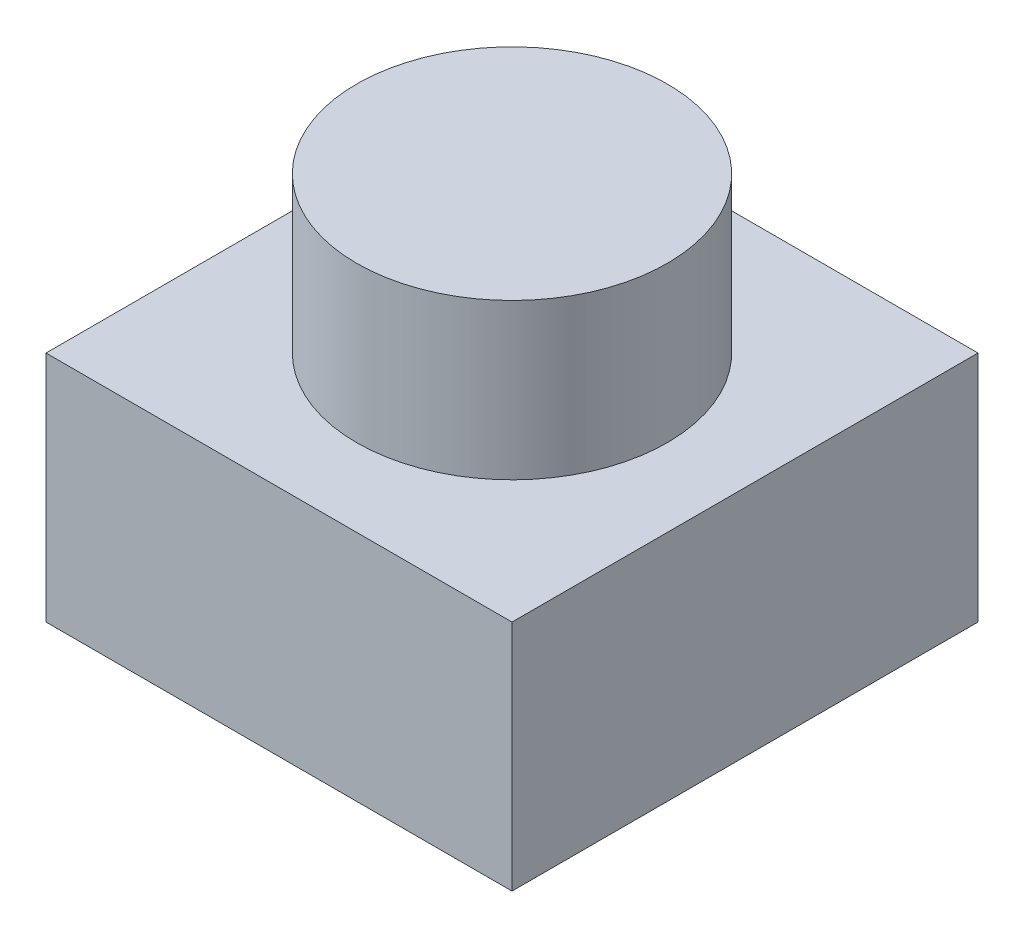
SolidWorks part; units mm, degrees
ref_plane "Front Plane" through (0, 0, 0) normal (0, 0, 1) x (1, 0, 0)
ref_plane "Top Plane" through (0, 0, 0) normal (0, 1, 0) x (1, 0, 0)
ref_plane "Right Plane" through (0, 0, 0) normal (1, 0, 0) x (0, 0, -1)
sketch "Sketch1" plane through (0, 0, 0) normal (0, 1, 0) x (1, 0, 0)
  line L1 (-3, -3) -> (3, -3)
  line L2 (-3, -3) -> (-3, 3)
  line L3 (-3, 3) -> (3, 3)
  line L4 (3, -3) -> (3, 3)
  line L5 (-3, -3) -> (3, 3) construction
  line L6 (-3, 3) -> (3, -3) construction
  point P0 (0, 0)
  dimension "D1" = 6
  dimension "D2" = 6
extrude "Boss-Extrude1" add sketch "Sketch1" along normal blind 3
sketch "Sketch2" plane through (0, 3, 0) normal (0, 1, 0) x (1, 0, 0)
  circle A0 centre (0, 0) radius 2
  dimension "D1" = 4
extrude "Boss-Extrude2" add sketch "Sketch2" along normal blind 2
